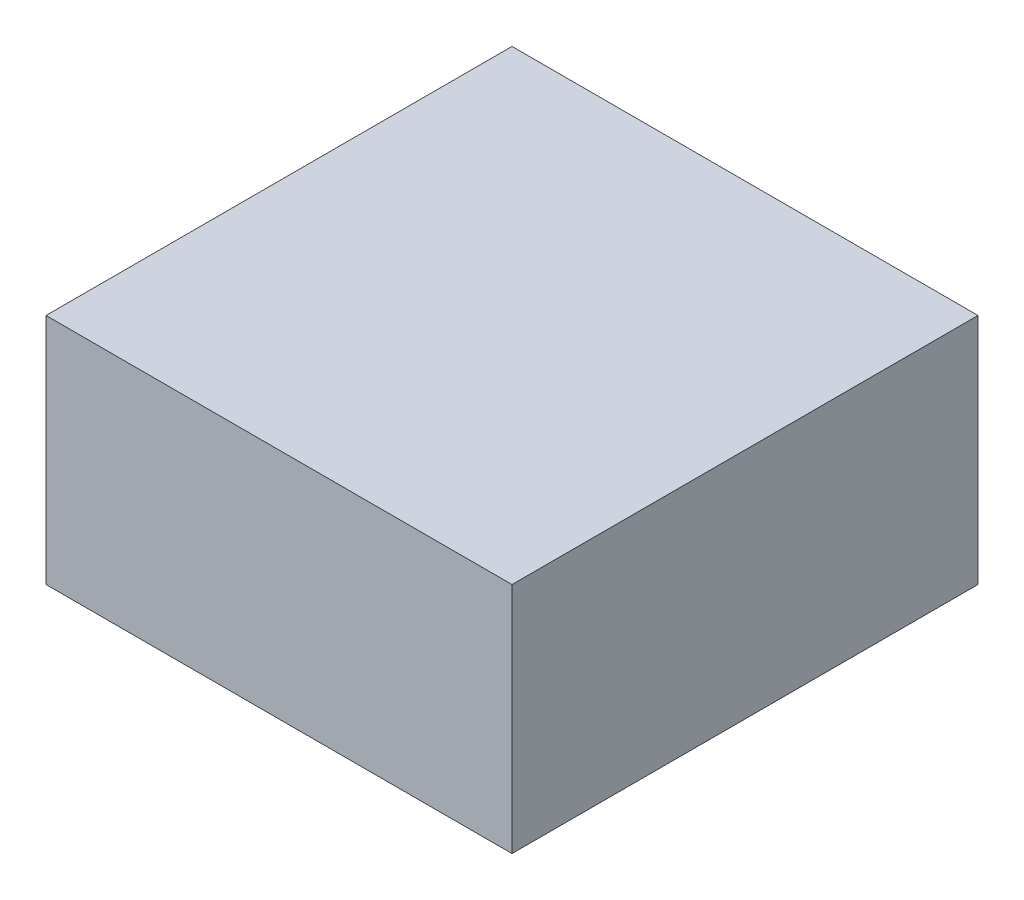
SolidWorks part; units mm, degrees
ref_plane "Front Plane" through (0, 0, 0) normal (0, 0, 1) x (1, 0, 0)
ref_plane "Top Plane" through (0, 0, 0) normal (0, 1, 0) x (1, 0, 0)
ref_plane "Right Plane" through (0, 0, 0) normal (1, 0, 0) x (0, 0, -1)
sketch "Sketch1" plane through (0, 0, 0) normal (0, 1, 0) x (1, 0, 0)
  line L1 (0, 0) -> (2, 0)
  line L2 (0, 0) -> (0, 2)
  line L3 (0, 2) -> (2, 2)
  line L4 (2, 0) -> (2, 2)
  dimension "D1" = 2
  dimension "D2" = 2
extrude "Boss-Extrude1" add sketch "Sketch1" along normal blind 1
